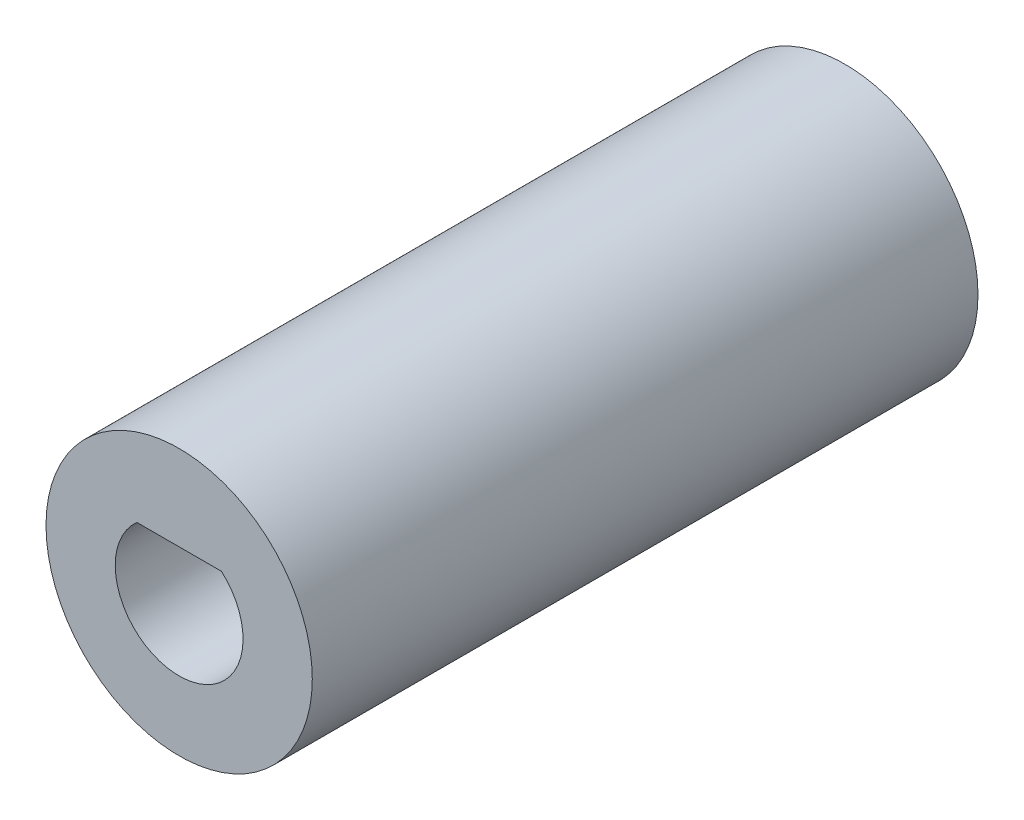
SolidWorks part; units mm, degrees
ref_plane "Front Plane" through (0, 0, 0) normal (0, 0, 1) x (1, 0, 0)
ref_plane "Top Plane" through (0, 0, 0) normal (0, 1, 0) x (1, 0, 0)
ref_plane "Right Plane" through (0, 0, 0) normal (1, 0, 0) x (0, 0, -1)
sketch "Sketch1" plane through (0, 0, 0) normal (0, 0, 1) x (1, 0, 0)
  circle A0 centre (0, 0) radius 6.35
  dimension "D1" = 12.7
extrude "Boss-Extrude1" add sketch "Sketch1" along normal blind 31.75
sketch "Sketch2" plane through (0, 0, 31.75) normal (0, 0, 1) x (1, 0, 0)
  line L0 (2.0161, 2.286) -> (-2.0161, 2.286)
  arc A0 (-2.0161, 2.286) -> (2.0161, 2.286) centre (0, 0) ccw
  dimension "D1" = 6.096
  dimension "D2" = 2.286
extrude "Cut-Extrude1" cut sketch "Sketch2" against normal blind 19.05
sketch "Sketch3" plane through (0, 0, 0) normal (0, 0, -1) x (-1, 0, 0)
  circle A0 centre (0, 0) radius 3.175
  point P2 (0, 0)
  dimension "D1" = 6.35
extrude "Cut-Extrude2" cut sketch "Sketch3" against normal blind 12.7
